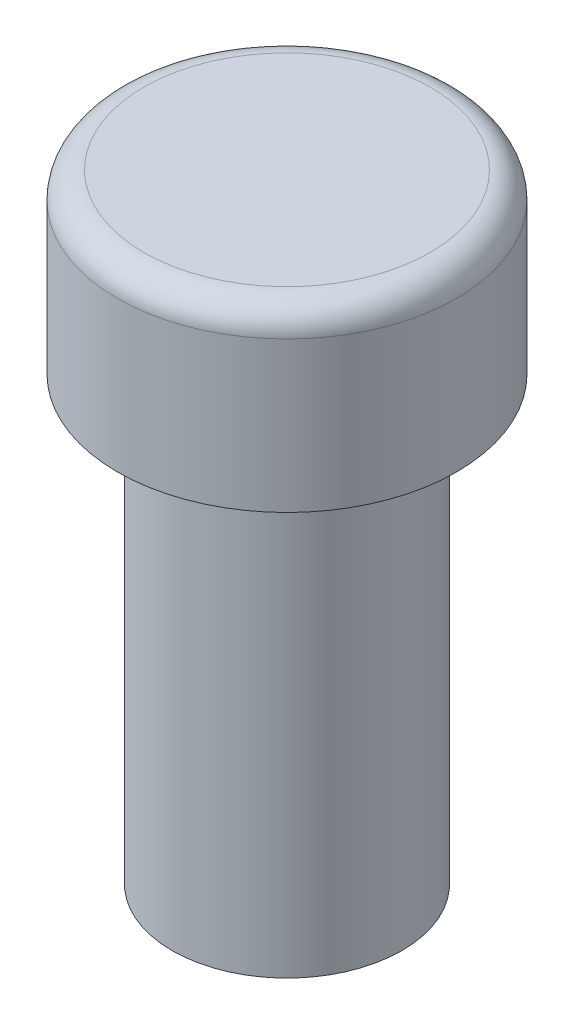
SolidWorks part; units mm, degrees
ref_plane "Front Plane" through (0, 0, 0) normal (0, 0, 1) x (1, 0, 0)
ref_plane "Top Plane" through (0, 0, 0) normal (0, 1, 0) x (1, 0, 0)
ref_plane "Right Plane" through (0, 0, 0) normal (1, 0, 0) x (0, 0, -1)
sketch "Sketch1" plane through (0, 0, 0) normal (0, 1, 0) x (1, 0, 0)
  circle A0 centre (0, 0) radius 3.25
  dimension "D1" = 6.5
extrude "Boss-Extrude1" add sketch "Sketch1" along normal blind 12.5 contours A0
sketch "Sketch2" plane through (0, 0, 0) normal (0, -1, 0) x (1, 0, 0)
  circle A1 centre (0, 0) radius 1.75
  dimension "D1" = 3.5
extrude "Cut-Extrude1" cut sketch "Sketch2" against normal blind 2.5
sketch "Sketch6" plane through (0, 12.5, 0) normal (0, 1, 0) x (1, 0, 0)
  circle A0 centre (0, 0) radius 4.8
  dimension "D1" = 9.6
extrude "Boss-Extrude2" add sketch "Sketch6" along normal blind 5 contours A0
fillet "Fillet1" radius 0.75 1 edges at (0, 17.5, 4.8)
